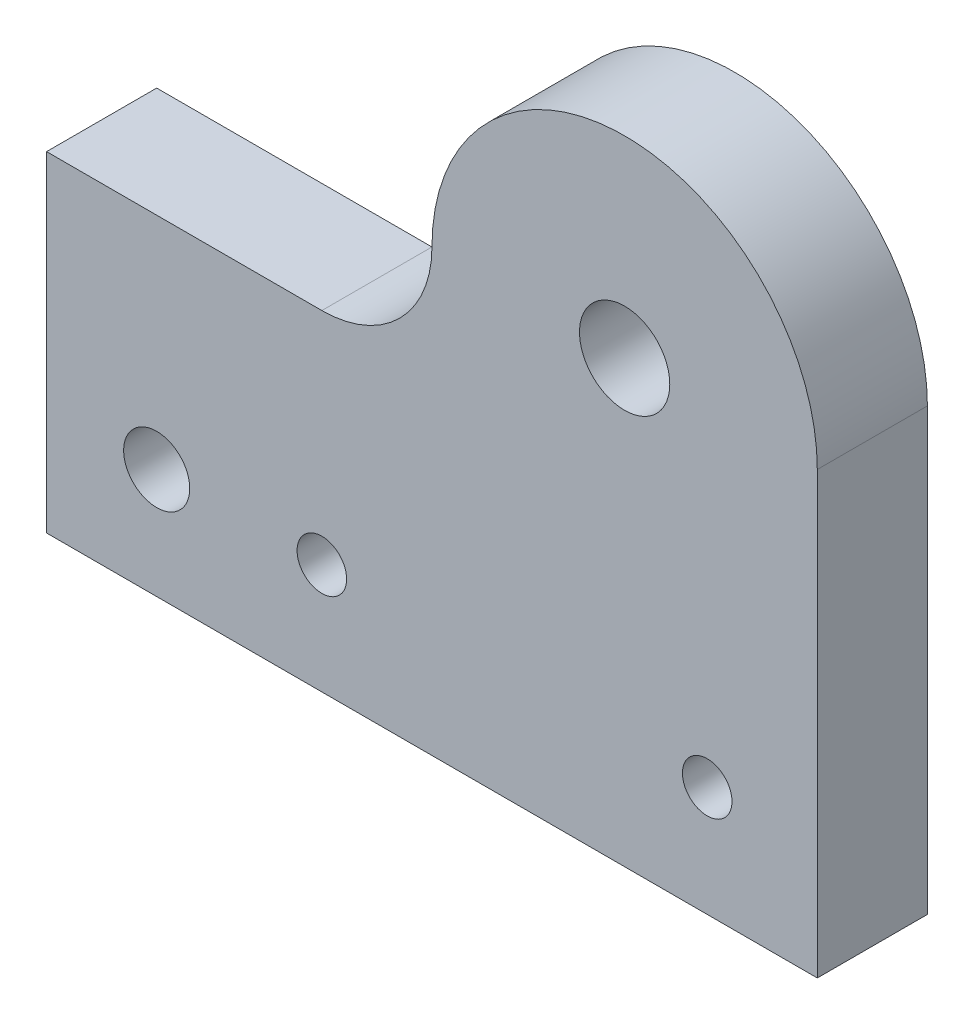
SolidWorks part; units mm, degrees
ref_plane "前视基准面" through (0, 0, 0) normal (0, 0, 1) x (1, 0, 0)
ref_plane "上视基准面" through (0, 0, 0) normal (0, 1, 0) x (1, 0, 0)
ref_plane "右视基准面" through (0, 0, 0) normal (1, 0, 0) x (0, 0, -1)
sketch "草图2" plane through (0, 0, 0) normal (0, 0, 1) x (1, 0, 0)
  line L0 (-51.1511, -5) -> (62.3741, -5) construction
  line L1 (-35, 15) -> (-10, 15)
  line L2 (-35, 15) -> (-35, -15)
  line L3 (-35, -15) -> (35, -15)
  line L4 (35, 15) -> (35, -15)
  line L5 (0, 36.7986) -> (0, -51.0432) construction
  line L8 (35, 25) -> (35, 15)
  arc A0 (35, 25) -> (0, 25) centre (17.5, 25) ccw
  arc A1 (-10, 15) -> (0, 25) centre (-10, 25) ccw
  circle A2 centre (17.5, 25) radius 4.1
  circle A3 centre (-25, -5) radius 3
  circle A4 centre (-10, -5) radius 2.25
  circle A5 centre (25, -5) radius 2.25
  point P15 (0, 15)
  dimension "D5" = 10
  dimension "D6" = 8.2
  dimension "D7" = 15
  dimension "D8" = 50
  dimension "D9" = 4.5
  dimension "D10" = 6
  dimension "D11" = 10
  dimension "D1" = 30
  dimension "D2" = 70
  dimension "D3" = 35
  dimension "D4" = 40
  dimension "D12" = 10
extrude "凸台-拉伸1" add sketch "草图2" along normal blind 10
